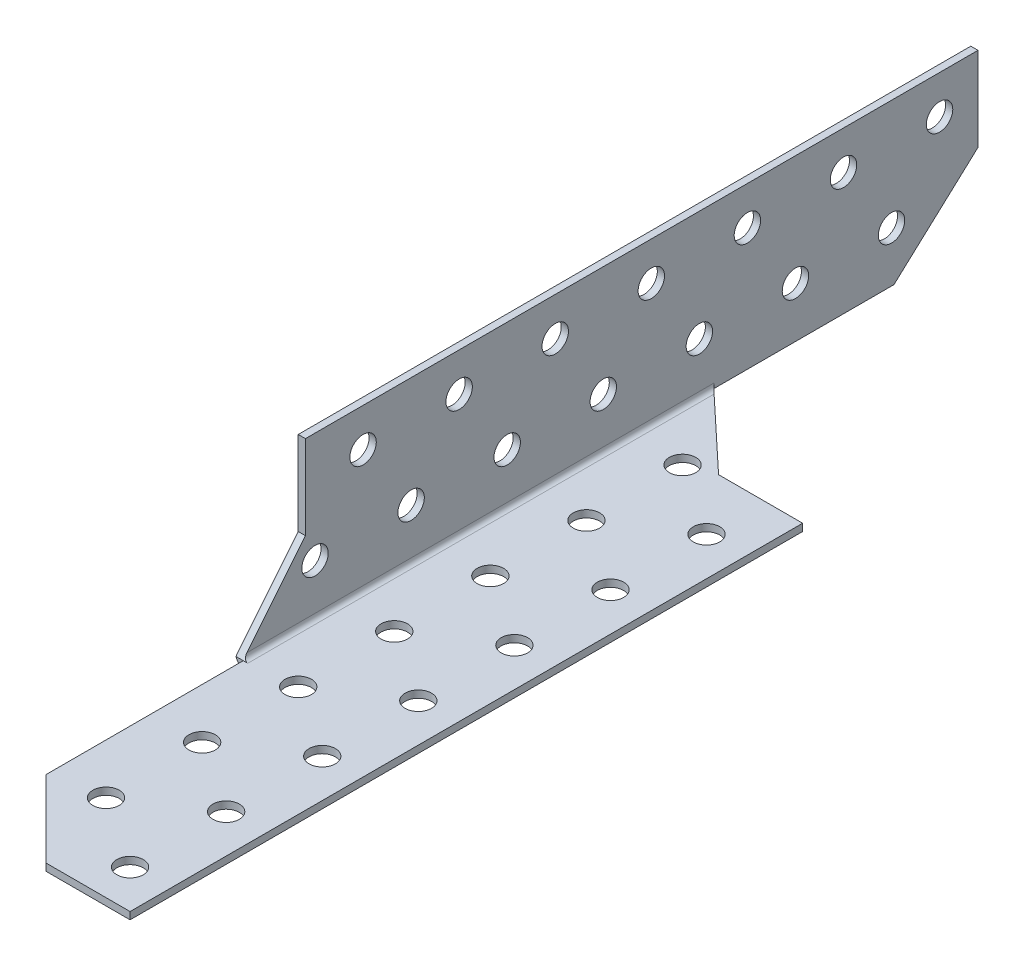
SolidWorks part; units mm, degrees
ref_plane "Płaszczyzna przednia" through (0, 0, 0) normal (0, 0, 1) x (1, 0, 0)
ref_plane "Płaszczyzna górna" through (0, 0, 0) normal (0, 1, 0) x (1, 0, 0)
ref_plane "Płaszczyzna prawa" through (0, 0, 0) normal (1, 0, 0) x (0, 0, -1)
sketch "Sketch1" plane through (0, 0, 0) normal (0, 0, 1) x (1, 0, 0)
  line L1 (-0.75, 17.5) -> (0.75, 17.5)
  line L2 (-0.75, 17.5) -> (-0.75, -17.5)
  line L3 (-0.75, -17.5) -> (0.75, -17.5)
  line L4 (0.75, 17.5) -> (0.75, -17.5)
  line L5 (-0.75, 17.5) -> (0.75, -17.5) construction
  line L6 (-0.75, -17.5) -> (0.75, 17.5) construction
  line L7 (-0.75, -17.5) -> (34.25, -17.5)
  line L8 (-0.75, -17.5) -> (-0.75, -16)
  line L9 (-0.75, -16) -> (34.25, -16)
  line L10 (34.25, -17.5) -> (34.25, -16)
  line L11 (-0.75, -17.5) -> (34.25, -16) construction
  line L12 (-0.75, -16) -> (34.25, -17.5) construction
  point P0 (0, 0)
  point P9 (16.75, -16.75)
  dimension "D1" = 1.5
  dimension "D2" = 35
  dimension "D3" = 1.5
  dimension "D4" = 35
extrude "Boss-Extrude1" add sketch "Sketch1" along normal blind 210 contours L2 L9 L4 L1 | L7 L10 L9 L4 | L9 L2 L3 L4
sketch "Sketch3" plane through (0.75, 0, 0) normal (1, 0, 0) x (0, 0, -1)
  line L0 (-140, 17.5) -> (-140, -16) construction
  line L1 (-210, 17.5) -> (0, 17.5) construction
  line L2 (-210, -16) -> (0, -16) construction
  line L3 (0, 17.5) -> (0, -16) construction
  line L4 (-140, 17.5) -> (-140, 0)
  line L5 (-153, 17.5) -> (-153, -16) construction
  line L6 (-210, 17.5) -> (-210, -16) construction
  line L7 (-153, -16) -> (-140, 0)
  line L8 (-140, 17.5) -> (-210, 17.5)
  line L9 (-210, 17.5) -> (-210, -16)
  line L10 (-210, -16) -> (-153, -16)
  line L11 (0, 0) -> (-17.5, -16)
  line L12 (-210, -16) -> (0, -16) construction
  line L13 (-17.5, -16) -> (-17.5, -36.8293)
  line L14 (-17.5, -36.8293) -> (0, -36.8293)
  line L15 (0, -36.8293) -> (0, 0)
  dimension "D1" = 140
  dimension "D2" = 17.5
  dimension "D3" = 57
  dimension "D4" = 17.5
extrude "Cut-Extrude2" cut sketch "Sketch3" against normal blind 62 and the other way blind 62
sketch "Sketch4" plane through (0, -16, 0) normal (0, 1, 0) x (1, 0, 0)
  line L0 (16.75, -210) -> (-0.75, -192.5)
  line L1 (-0.75, -210) -> (34.25, -210) construction
  line L2 (-0.75, -153) -> (-0.75, -210) construction
  line L3 (16.75, -210) -> (-0.75, -210)
  line L4 (-0.75, -210) -> (-0.75, -192.5)
  line L5 (34.25, -70) -> (0.75, -70) construction
  line L6 (34.25, -210) -> (34.25, -17.5) construction
  line L7 (0.75, -153) -> (0.75, -17.5) construction
  line L8 (34.25, -70) -> (16.75, -70)
  line L9 (16.75, -70) -> (0.75, -55)
  line L10 (0.75, -55) -> (0.75, -17.5)
  line L11 (0.75, -17.5) -> (34.25, -17.5)
  line L12 (34.25, -17.5) -> (34.25, -70)
  dimension "D1" = 17.5
  dimension "D2" = 140
  dimension "D3" = 17.5
  dimension "D4" = 155
extrude "Cut-Extrude3" cut sketch "Sketch4" against normal blind 62
sketch "Sketch5" plane through (0.75, 0, 0) normal (1, 0, 0) x (0, 0, -1)
  line L0 (0, 17.5) -> (0, 0) construction
  line L1 (-140, 17.5) -> (0, 17.5) construction
  line L2 (-8, 9.5) -> (-140, 9.5) construction
  line L3 (-140, 17.5) -> (-140, 0) construction
  line L4 (-144.4688, -5.5) -> (-6.0156, -5.5) construction
  line L5 (-140, 0) -> (-153, -16) construction
  line L6 (-17.5, -16) -> (0, 0) construction
  line L7 (-28, 9.5) -> (-28, -5.5) construction
  circle A0 centre (-8, 9.5) radius 2.75
  circle A1 centre (-28, 9.5) radius 2.75
  circle A2 centre (-48, 9.5) radius 2.75
  circle A3 centre (-68, 9.5) radius 2.75
  circle A4 centre (-88, 9.5) radius 2.75
  circle A5 centre (-108, 9.5) radius 2.75
  circle A6 centre (-128, 9.5) radius 2.75
  circle A7 centre (-18, -5.5) radius 2.75
  circle A8 centre (-38, -5.5) radius 2.75
  circle A9 centre (-58, -5.5) radius 2.75
  circle A10 centre (-78, -5.5) radius 2.75
  circle A11 centre (-98, -5.5) radius 2.75
  circle A12 centre (-118, -5.5) radius 2.75
  circle A13 centre (-138, -5.5) radius 2.75
  dimension "D1" = 8
  dimension "D3" = 20
  dimension "D12" = 20
  dimension "D2" = 8
  dimension "D4" = 20
  dimension "D5" = 20
  dimension "D6" = 20
  dimension "D7" = 20
  dimension "D8" = 20
  dimension "D9" = 12
  dimension "D10" = 8
  dimension "D11" = 23
  dimension "D13" = 20
  dimension "D14" = 20
  dimension "D15" = 20
  dimension "D16" = 20
  dimension "D17" = 20
  dimension "D18" = 10
extrude "Cut-Extrude4" cut sketch "Sketch5" against normal blind 5
fillet "Fillet1" radius 1 1 edges at (0.75, -16, 104)
fillet "Fillet2" radius 2 1 edges at (-0.75, -17.5, 105)
sketch "Sketch6" plane through (0.75, 0, 0) normal (1, 0, 0) x (0, 0, -1)
  line L1 (-55, -17.4365) -> (-17.5, -17.4365)
  line L2 (-55, -17.4365) -> (-55, -16)
  line L3 (-55, -16) -> (-17.5, -16)
  line L4 (-17.5, -17.4365) -> (-17.5, -16)
  line L5 (-55, -17.4365) -> (-17.5, -16) construction
  line L6 (-55, -16) -> (-17.5, -17.4365) construction
  point P4 (-36.25, -16.7182)
extrude "Cut-Extrude5" cut sketch "Sketch6" against normal blind 5
sketch "Sketch7" plane through (0, -16, 0) normal (0, 1, 0) x (1, 0, 0)
  line L1 (-0.6865, -153) -> (0.8135, -153)
  line L2 (-0.6865, -153) -> (-0.6865, -198.3598)
  line L3 (-0.6865, -198.3598) -> (0.8135, -198.3598)
  line L4 (0.8135, -153) -> (0.8135, -198.3598)
  line L5 (-0.6865, -153) -> (0.8135, -198.3598) construction
  line L6 (-0.6865, -198.3598) -> (0.8135, -153) construction
  point P4 (0.0635, -175.6799)
  dimension "D1" = 1.5
extrude "Cut-Extrude6" cut sketch "Sketch7" against normal blind 5
sketch "Sketch8" plane through (0, -16, 0) normal (0, 1, 0) x (1, 0, 0)
  line L0 (11.25, -72) -> (11.25, -201.8481) construction
  line L1 (26.25, -206.3168) -> (26.25, -67.8637) construction
  line L2 (11.25, -92) -> (26.25, -92) construction
  line L3 (34.25, -210) -> (34.25, -70) construction
  line L4 (16.75, -210) -> (34.25, -210) construction
  circle A0 centre (11.25, -72) radius 2.75
  circle A1 centre (11.25, -92) radius 2.75
  circle A2 centre (11.25, -112) radius 2.75
  circle A3 centre (11.25, -132) radius 2.75
  circle A4 centre (11.25, -152) radius 2.75
  circle A5 centre (11.25, -172) radius 2.75
  circle A6 centre (11.25, -192) radius 2.75
  circle A7 centre (26.25, -82) radius 2.75
  circle A8 centre (26.25, -102) radius 2.75
  circle A9 centre (26.25, -122) radius 2.75
  circle A10 centre (26.25, -142) radius 2.75
  circle A11 centre (26.25, -162) radius 2.75
  circle A12 centre (26.25, -182) radius 2.75
  circle A13 centre (26.25, -202) radius 2.75
  dimension "D1" = 20
  dimension "D2" = 20
  dimension "D3" = 20
  dimension "D4" = 20
  dimension "D5" = 20
  dimension "D6" = 20
  dimension "D7" = 20
  dimension "D8" = 20
  dimension "D9" = 20
  dimension "D10" = 20
  dimension "D11" = 20
  dimension "D12" = 20
  dimension "D13" = 10
  dimension "D14" = 8
  dimension "D15" = 23
  dimension "D16" = 15
  dimension "D17" = 8
extrude "Cut-Extrude7" cut sketch "Sketch8" against normal blind 5
